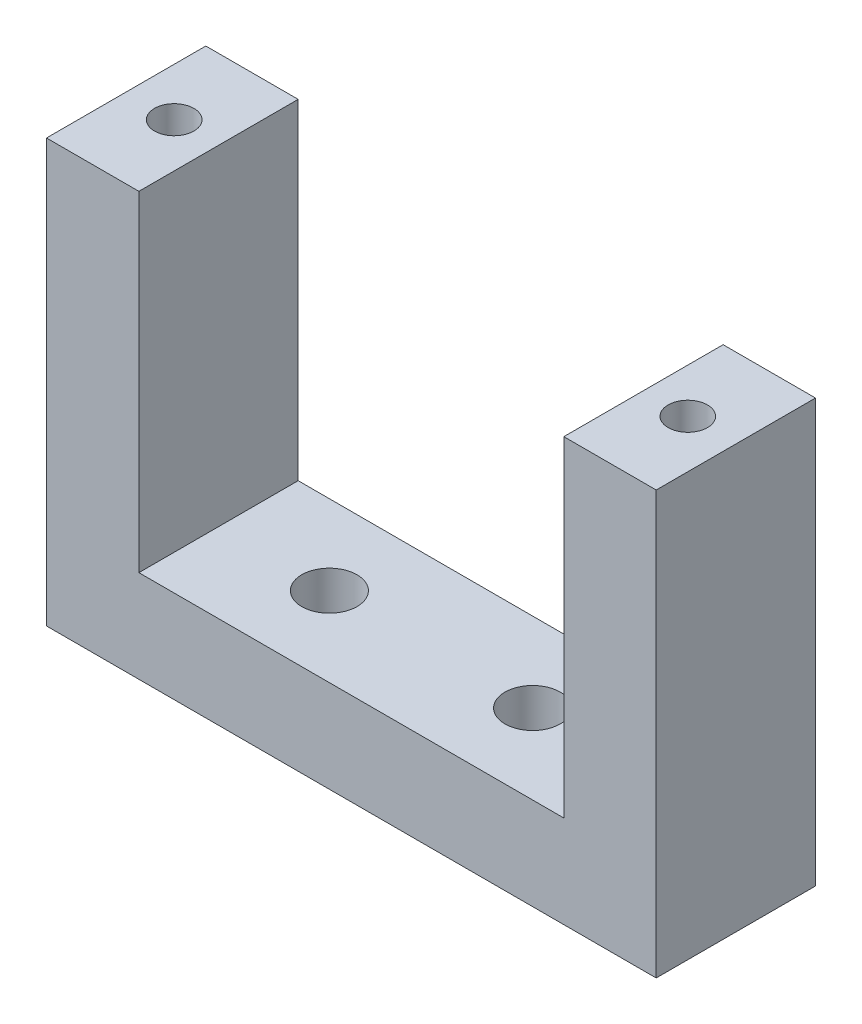
SolidWorks part; units mm, degrees
ref_plane "Front Plane" through (0, 0, 0) normal (0, 0, 1) x (1, 0, 0)
ref_plane "Top Plane" through (0, 0, 0) normal (0, 1, 0) x (1, 0, 0)
ref_plane "Right Plane" through (0, 0, 0) normal (1, 0, 0) x (0, 0, -1)
sketch "Sketch1" plane through (0, 0, 0) normal (0, 0, 1) x (1, 0, 0)
  line L0 (-20.955, 22.7018) -> (-14.605, 22.7018)
  line L1 (-14.605, 0) -> (-14.605, 22.7018)
  line L2 (-14.605, 0) -> (14.605, 0)
  line L3 (14.605, 0) -> (14.605, 22.7018)
  line L4 (14.605, 22.7018) -> (20.955, 22.7018)
  line L5 (20.955, 22.7018) -> (20.955, -6.35)
  line L6 (20.955, -6.35) -> (-20.955, -6.35)
  line L7 (-20.955, -6.35) -> (-20.955, 22.7018)
  line L8 (-14.605, 0) -> (14.605, 0)
  line L9 (14.605, 0) -> (-14.605, 0)
  dimension "D1" = 6.35
  dimension "D2" = 29.0518
  dimension "D3" = 6.35
  dimension "D4" = 41.91
  dimension "D5" = 6.35
extrude "Boss-Extrude1" add sketch "Sketch1" along normal blind 10.95 contours L7 L8 L1 L0 | L8 L7 L6 L5 L2 | L3 L8 L5 L4
hole_wizard "#6 Clearance Hole1" positions "Sketch4" profile "Sketch5" hole size "#6" standard "ANSI Inch" end condition through all
sketch "Sketch4" plane through (0, -6.35, 0) normal (0, -1, 0) x (-1, 0, 0)
  line L0 (-20.955, -5.475) -> (-6.985, -5.475) construction
  line L1 (-20.955, -10.95) -> (-20.955, 0) construction
  line L2 (-6.985, -5.475) -> (6.985, -5.475) construction
  line L3 (6.985, -5.475) -> (20.955, -5.475) construction
  line L4 (20.955, -10.95) -> (20.955, 0) construction
  point P2 (-6.985, -5.475)
  point P5 (6.985, -5.475)
sketch "Sketch5" plane through (6.985, -6.35, 5.475) normal (1, 0, 0) x (0, 0, -1)
  line L0 (0, 0) -> (0, 29.0518)
  line L1 (0, 29.0518) -> (1.8986, 29.0518)
  line L2 (1.8986, 29.0518) -> (1.8986, 0)
  line L5 (1.8986, 0) -> (0, 0)
  line L11 (0, -6.35) -> (0, 107.95) construction
  dimension "Thru Hole Dia." = 3.7973
  dimension "Thru Hole Depth" = 29.0518
hole_wizard "#6-32 Tapped Hole1" positions "Sketch7" profile "Sketch8" tap size "#6-32" standard "ANSI Inch"
sketch "Sketch7" plane through (0, 22.7018, 0) normal (0, 1, 0) x (1, 0, 0)
  line L12 (20.955, -5.475) -> (17.653, -5.475) construction
  line L13 (20.955, -10.95) -> (20.955, 0) construction
  line L14 (17.653, -5.475) -> (-17.653, -5.475) construction
  line L15 (-17.653, -5.475) -> (-20.955, -5.475) construction
  line L16 (-20.955, -10.95) -> (-20.955, 0) construction
  point P26 (17.653, -5.475)
  point P28 (-17.653, -5.475)
  dimension "D1" = 35.306
sketch "Sketch8" plane through (17.653, 22.7018, 5.475) normal (1, 0, 0) x (0, 0, 1)
  line L0 (0, 0) -> (0, 10.2107)
  line L1 (0, 10.2107) -> (1.3525, 9.398)
  line L2 (1.3525, 9.398) -> (1.3525, 0)
  line L5 (1.3525, 0) -> (0, 0)
  line L10 (0, 10.2107) -> (-1.3525, 9.398) construction
  line L11 (0, -6.35) -> (0, 107.95) construction
  dimension "Tap Drill Dia." = 2.7051
  dimension "Tap Drill Depth" = 9.398
  dimension "Drill Angle" = 118
